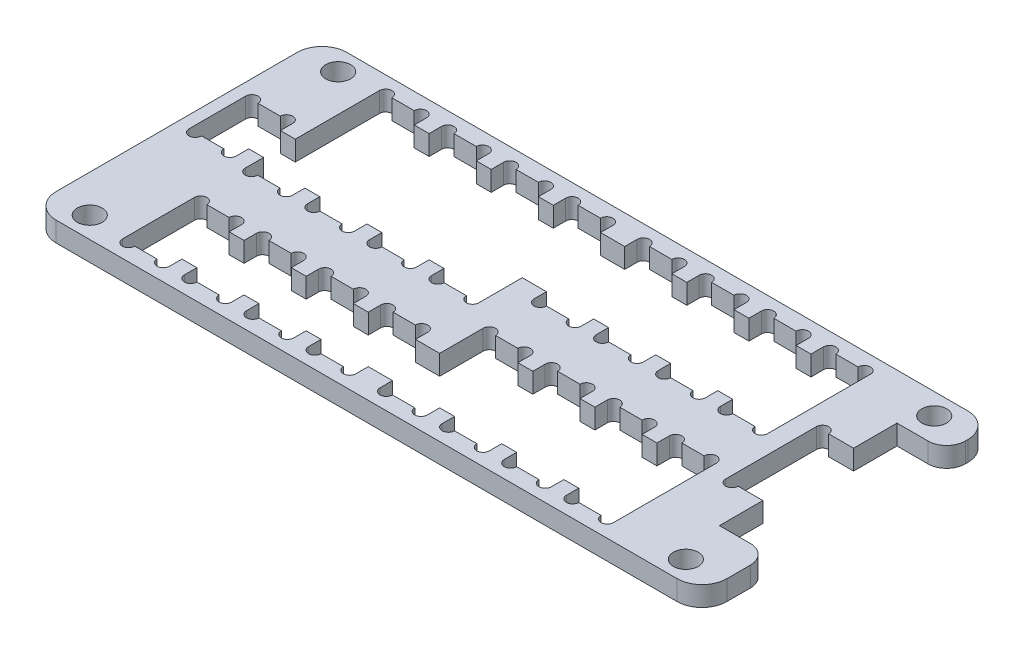
SolidWorks part; units mm, degrees
ref_plane "Plan de face" through (0, 0, 0) normal (0, 0, 1) x (1, 0, 0)
ref_plane "Plan de dessus" through (0, 0, 0) normal (0, 1, 0) x (1, 0, 0)
ref_plane "Plan de droite" through (0, 0, 0) normal (1, 0, 0) x (0, 0, -1)
sketch "Esquisse1" plane through (0, 0, 0) normal (0, 1, 0) x (1, 0, 0)
  line L0 (-151, -90) -> (-97, -90) construction
  line L1 (-124, -78.3) -> (-124, -101.7) construction
  line L3 (-149, -101.7) -> (-99, -101.7)
  line L4 (-151, -99.7) -> (-151, -80.3)
  line L5 (-149, -78.3) -> (-99, -78.3)
  line L6 (-97, -99.7) -> (-97, -80.3)
  line L7 (-151, -101.7) -> (-97, -78.3) construction
  line L8 (-151, -78.3) -> (-97, -101.7) construction
  circle A0 centre (-100, -80) radius 1
  circle A1 centre (-100, -100) radius 1
  circle A2 centre (-148, -100) radius 1
  circle A3 centre (-148, -80) radius 1
  arc A4 (-151, -99.7) -> (-149, -101.7) centre (-149, -99.7) ccw
  arc A5 (-99, -101.7) -> (-97, -99.7) centre (-99, -99.7) ccw
  arc A6 (-97, -80.3) -> (-99, -78.3) centre (-99, -80.3) ccw
  arc A7 (-149, -78.3) -> (-151, -80.3) centre (-149, -80.3) ccw
  point P14 (-124, -90)
  dimension "D5" = 2
  dimension "D8" = 2
  dimension "D1" = 48
  dimension "D2" = 20
  dimension "D3" = 23.4
  dimension "D4" = 54
  dimension "D6" = 80
  dimension "D7" = 148
extrude "base" add sketch "Esquisse1" along normal blind 1.6
sketch "Esquisse2" plane through (0, 0, 0) normal (0, 1, 0) x (1, 0, 0)
  line L0 (-147.35, -85.625) -> (-147.35, -89.875) construction
  line L1 (-147.227, -89.975) -> (-149.023, -89.975)
  line L2 (-146.225, -89.975) -> (-146.225, -85.425)
  line L3 (-147.227, -85.425) -> (-149.023, -85.425)
  line L4 (-150.025, -89.975) -> (-150.025, -85.425)
  line L5 (-146.225, -87.7) -> (-150.025, -87.7) construction
  line L6 (-142.35, -68.9568) -> (-142.35, -111.0917) construction
  line L7 (-141.225, -97.45) -> (-145.025, -97.45) construction
  line L8 (-144.023, -79.65) -> (-142.227, -79.65)
  line L9 (-145.025, -79.65) -> (-145.025, -90.45)
  line L10 (-144.023, -90.45) -> (-142.227, -90.45)
  line L11 (-141.225, -79.65) -> (-141.225, -90.45)
  line L12 (-144.023, -94.55) -> (-142.227, -94.55)
  line L13 (-145.025, -94.55) -> (-145.025, -100.35)
  line L14 (-144.023, -100.35) -> (-142.227, -100.35)
  line L15 (-141.225, -94.55) -> (-141.225, -100.35)
  line L16 (-141.225, -85.05) -> (-145.025, -85.05) construction
  line L17 (-143.125, -90.3) -> (-143.125, -88.6205) construction
  line L18 (-143.125, -100.2) -> (-143.125, -98.5773) construction
  line L19 (-136.225, -79.65) -> (-136.225, -90.45)
  line L20 (-139.023, -90.45) -> (-137.227, -90.45)
  line L21 (-140.025, -79.65) -> (-140.025, -90.45)
  line L22 (-139.023, -79.65) -> (-137.227, -79.65)
  line L23 (-136.225, -94.55) -> (-136.225, -100.35)
  line L24 (-139.023, -100.35) -> (-137.227, -100.35)
  line L25 (-140.025, -94.55) -> (-140.025, -100.35)
  line L26 (-139.023, -94.55) -> (-137.227, -94.55)
  line L27 (-131.225, -79.65) -> (-131.225, -90.45)
  line L28 (-134.023, -90.45) -> (-132.227, -90.45)
  line L29 (-135.025, -79.65) -> (-135.025, -90.45)
  line L30 (-134.023, -79.65) -> (-132.227, -79.65)
  line L31 (-131.225, -94.55) -> (-131.225, -100.35)
  line L32 (-134.023, -100.35) -> (-132.227, -100.35)
  line L33 (-135.025, -94.55) -> (-135.025, -100.35)
  line L34 (-134.023, -94.55) -> (-132.227, -94.55)
  line L35 (-126.225, -79.65) -> (-126.225, -90.45)
  line L36 (-129.023, -90.45) -> (-127.227, -90.45)
  line L37 (-130.025, -79.65) -> (-130.025, -90.45)
  line L38 (-129.023, -79.65) -> (-127.227, -79.65)
  line L39 (-126.225, -94.55) -> (-126.225, -100.35)
  line L40 (-129.023, -100.35) -> (-127.227, -100.35)
  line L41 (-130.025, -94.55) -> (-130.025, -100.35)
  line L42 (-129.023, -94.55) -> (-127.227, -94.55)
  line L43 (-141.225, -79.65) -> (-136.225, -79.65) construction
  line L44 (-121.6, -78.3) -> (-121.6, -101.7) construction
  line L45 (-99, -78.3) -> (-149, -78.3) construction
  line L46 (-149, -101.7) -> (-99, -101.7) construction
  line L47 (-121.6, -90) -> (-105.675, -90) construction
  line L48 (-122.375, -79.65) -> (-122.375, -82.0443) construction
  line L49 (-121.477, -79.65) -> (-123.273, -79.65)
  line L50 (-120.475, -79.65) -> (-120.475, -87.95)
  line L51 (-121.477, -87.95) -> (-123.273, -87.95)
  line L52 (-124.275, -79.65) -> (-124.275, -87.95)
  line L53 (-124.275, -83.8) -> (-120.475, -83.8) construction
  line L54 (-121.477, -100.35) -> (-123.273, -100.35)
  line L55 (-124.275, -100.35) -> (-124.275, -92.05)
  line L56 (-121.477, -92.05) -> (-123.273, -92.05)
  line L57 (-120.475, -100.35) -> (-120.475, -92.05)
  line L58 (-119.275, -79.65) -> (-119.275, -87.95)
  line L59 (-116.477, -87.95) -> (-118.273, -87.95)
  line L60 (-115.475, -79.65) -> (-115.475, -87.95)
  line L61 (-116.477, -79.65) -> (-118.273, -79.65)
  line L62 (-119.275, -100.35) -> (-119.275, -92.05)
  line L63 (-116.477, -92.05) -> (-118.273, -92.05)
  line L64 (-115.475, -100.35) -> (-115.475, -92.05)
  line L65 (-116.477, -100.35) -> (-118.273, -100.35)
  line L66 (-114.275, -79.65) -> (-114.275, -87.95)
  line L67 (-111.477, -87.95) -> (-113.273, -87.95)
  line L68 (-110.475, -79.65) -> (-110.475, -87.95)
  line L69 (-111.477, -79.65) -> (-113.273, -79.65)
  line L70 (-114.275, -100.35) -> (-114.275, -92.05)
  line L71 (-111.477, -92.05) -> (-113.273, -92.05)
  line L72 (-110.475, -100.35) -> (-110.475, -92.05)
  line L73 (-111.477, -100.35) -> (-113.273, -100.35)
  line L74 (-109.275, -79.65) -> (-109.275, -87.95)
  line L75 (-106.477, -87.95) -> (-108.273, -87.95)
  line L76 (-105.475, -79.65) -> (-105.475, -87.95)
  line L77 (-106.477, -79.65) -> (-108.273, -79.65)
  line L78 (-109.275, -100.35) -> (-109.275, -92.05)
  line L79 (-106.477, -92.05) -> (-108.273, -92.05)
  line L80 (-105.475, -100.35) -> (-105.475, -92.05)
  line L81 (-106.477, -100.35) -> (-108.273, -100.35)
  line L82 (-124.275, -79.65) -> (-119.275, -79.65) construction
  line L83 (-97, -99.7) -> (-97, -80.3) construction
  line L84 (-100.998, -85.5) -> (-102.998, -85.5)
  line L85 (-97, -80.5) -> (-97, -97.8)
  line L86 (-100.998, -92.8) -> (-102.998, -92.8)
  line L87 (-104, -85.5) -> (-104, -92.8)
  line L88 (-104, -89.15) -> (-97, -89.15) construction
  line L89 (-100.9, -85.5) -> (-100.9, -92.8) construction
  line L90 (-147.35, -86.6711) -> (-150.025, -86.6711) construction
  line L91 (-142.35, -96.0769) -> (-145.025, -96.0769) construction
  line L92 (-121.6, -84.5733) -> (-124.275, -84.5733) construction
  line L93 (-100.998, -85.5) -> (-100.998, -82)
  line L94 (-100.998, -82) -> (-98.5, -82)
  line L95 (-97, -99.7) -> (-97, -80.3) construction
  line L97 (-100.998, -96.3) -> (-98.5, -96.3)
  line L98 (-100.998, -92.8) -> (-100.998, -96.3)
  arc A0 (-150.025, -85.425) -> (-149.023, -85.425) centre (-149.524, -85.425) cw
  arc A1 (-146.225, -85.425) -> (-147.227, -85.425) centre (-146.726, -85.425) ccw
  arc A2 (-146.225, -89.975) -> (-147.227, -89.975) centre (-146.726, -89.975) cw
  arc A3 (-150.025, -89.975) -> (-149.023, -89.975) centre (-149.524, -89.975) ccw
  arc A4 (-145.025, -79.65) -> (-144.023, -79.65) centre (-144.524, -79.65) cw
  arc A5 (-141.225, -79.65) -> (-142.227, -79.65) centre (-141.726, -79.65) ccw
  arc A6 (-145.025, -90.45) -> (-144.023, -90.45) centre (-144.524, -90.45) ccw
  arc A7 (-141.225, -90.45) -> (-142.227, -90.45) centre (-141.726, -90.45) cw
  arc A8 (-145.025, -94.55) -> (-144.023, -94.55) centre (-144.524, -94.55) cw
  arc A9 (-141.225, -94.55) -> (-142.227, -94.55) centre (-141.726, -94.55) ccw
  arc A10 (-145.025, -100.35) -> (-144.023, -100.35) centre (-144.524, -100.35) ccw
  arc A11 (-141.225, -100.35) -> (-142.227, -100.35) centre (-141.726, -100.35) cw
  arc A12 (-136.225, -90.45) -> (-137.227, -90.45) centre (-136.726, -90.45) cw
  arc A13 (-140.025, -90.45) -> (-139.023, -90.45) centre (-139.524, -90.45) ccw
  arc A14 (-140.025, -79.65) -> (-139.023, -79.65) centre (-139.524, -79.65) cw
  arc A15 (-136.225, -79.65) -> (-137.227, -79.65) centre (-136.726, -79.65) ccw
  arc A16 (-136.225, -100.35) -> (-137.227, -100.35) centre (-136.726, -100.35) cw
  arc A17 (-140.025, -100.35) -> (-139.023, -100.35) centre (-139.524, -100.35) ccw
  arc A18 (-140.025, -94.55) -> (-139.023, -94.55) centre (-139.524, -94.55) cw
  arc A19 (-136.225, -94.55) -> (-137.227, -94.55) centre (-136.726, -94.55) ccw
  arc A20 (-131.225, -90.45) -> (-132.227, -90.45) centre (-131.726, -90.45) cw
  arc A21 (-135.025, -90.45) -> (-134.023, -90.45) centre (-134.524, -90.45) ccw
  arc A22 (-135.025, -79.65) -> (-134.023, -79.65) centre (-134.524, -79.65) cw
  arc A23 (-131.225, -79.65) -> (-132.227, -79.65) centre (-131.726, -79.65) ccw
  arc A24 (-131.225, -100.35) -> (-132.227, -100.35) centre (-131.726, -100.35) cw
  arc A25 (-135.025, -100.35) -> (-134.023, -100.35) centre (-134.524, -100.35) ccw
  arc A26 (-135.025, -94.55) -> (-134.023, -94.55) centre (-134.524, -94.55) cw
  arc A27 (-131.225, -94.55) -> (-132.227, -94.55) centre (-131.726, -94.55) ccw
  arc A28 (-126.225, -90.45) -> (-127.227, -90.45) centre (-126.726, -90.45) cw
  arc A29 (-130.025, -90.45) -> (-129.023, -90.45) centre (-129.524, -90.45) ccw
  arc A30 (-130.025, -79.65) -> (-129.023, -79.65) centre (-129.524, -79.65) cw
  arc A31 (-126.225, -79.65) -> (-127.227, -79.65) centre (-126.726, -79.65) ccw
  arc A32 (-126.225, -100.35) -> (-127.227, -100.35) centre (-126.726, -100.35) cw
  arc A33 (-130.025, -100.35) -> (-129.023, -100.35) centre (-129.524, -100.35) ccw
  arc A34 (-130.025, -94.55) -> (-129.023, -94.55) centre (-129.524, -94.55) cw
  arc A35 (-126.225, -94.55) -> (-127.227, -94.55) centre (-126.726, -94.55) ccw
  arc A36 (-124.275, -79.65) -> (-123.273, -79.65) centre (-123.774, -79.65) cw
  arc A37 (-120.475, -79.65) -> (-121.477, -79.65) centre (-120.976, -79.65) ccw
  arc A38 (-120.475, -87.95) -> (-121.477, -87.95) centre (-120.976, -87.95) cw
  arc A39 (-124.275, -87.95) -> (-123.273, -87.95) centre (-123.774, -87.95) ccw
  arc A40 (-120.475, -100.35) -> (-121.477, -100.35) centre (-120.976, -100.35) cw
  arc A41 (-124.275, -100.35) -> (-123.273, -100.35) centre (-123.774, -100.35) ccw
  arc A42 (-124.275, -92.05) -> (-123.273, -92.05) centre (-123.774, -92.05) cw
  arc A43 (-120.475, -92.05) -> (-121.477, -92.05) centre (-120.976, -92.05) ccw
  arc A44 (-119.275, -87.95) -> (-118.273, -87.95) centre (-118.774, -87.95) ccw
  arc A45 (-115.475, -87.95) -> (-116.477, -87.95) centre (-115.976, -87.95) cw
  arc A46 (-115.475, -79.65) -> (-116.477, -79.65) centre (-115.976, -79.65) ccw
  arc A47 (-119.275, -79.65) -> (-118.273, -79.65) centre (-118.774, -79.65) cw
  arc A48 (-119.275, -92.05) -> (-118.273, -92.05) centre (-118.774, -92.05) cw
  arc A49 (-115.475, -92.05) -> (-116.477, -92.05) centre (-115.976, -92.05) ccw
  arc A50 (-115.475, -100.35) -> (-116.477, -100.35) centre (-115.976, -100.35) cw
  arc A51 (-119.275, -100.35) -> (-118.273, -100.35) centre (-118.774, -100.35) ccw
  arc A52 (-114.275, -87.95) -> (-113.273, -87.95) centre (-113.774, -87.95) ccw
  arc A53 (-110.475, -87.95) -> (-111.477, -87.95) centre (-110.976, -87.95) cw
  arc A54 (-110.475, -79.65) -> (-111.477, -79.65) centre (-110.976, -79.65) ccw
  arc A55 (-114.275, -79.65) -> (-113.273, -79.65) centre (-113.774, -79.65) cw
  arc A56 (-114.275, -92.05) -> (-113.273, -92.05) centre (-113.774, -92.05) cw
  arc A57 (-110.475, -92.05) -> (-111.477, -92.05) centre (-110.976, -92.05) ccw
  arc A58 (-110.475, -100.35) -> (-111.477, -100.35) centre (-110.976, -100.35) cw
  arc A59 (-114.275, -100.35) -> (-113.273, -100.35) centre (-113.774, -100.35) ccw
  arc A60 (-109.275, -87.95) -> (-108.273, -87.95) centre (-108.774, -87.95) ccw
  arc A61 (-105.475, -87.95) -> (-106.477, -87.95) centre (-105.976, -87.95) cw
  arc A62 (-105.475, -79.65) -> (-106.477, -79.65) centre (-105.976, -79.65) ccw
  arc A63 (-109.275, -79.65) -> (-108.273, -79.65) centre (-108.774, -79.65) cw
  arc A64 (-109.275, -92.05) -> (-108.273, -92.05) centre (-108.774, -92.05) cw
  arc A65 (-105.475, -92.05) -> (-106.477, -92.05) centre (-105.976, -92.05) ccw
  arc A66 (-105.475, -100.35) -> (-106.477, -100.35) centre (-105.976, -100.35) cw
  arc A67 (-109.275, -100.35) -> (-108.273, -100.35) centre (-108.774, -100.35) ccw
  arc A68 (-104, -85.5) -> (-102.998, -85.5) centre (-103.499, -85.5) cw
  arc A69 (-104, -92.8) -> (-102.998, -92.8) centre (-103.499, -92.8) ccw
  arc A70 (-98.5, -82) -> (-97, -80.5) centre (-98.5, -80.5) ccw
  arc A71 (-98.5, -96.3) -> (-97, -97.8) centre (-98.5, -97.8) cw
  point P152 (-122.375, -87.95)
  point P264 (-97, -81.1652)
  point P266 (-97, -81.3019)
  point P267 (0, 0)
  point P271 (0, 0)
  dimension "D13" = 0.501
  dimension "D26" = 1.5
  dimension "D1" = 4.55
  dimension "D2" = 2.675
  dimension "D3" = 3.8
  dimension "D4" = 147.35
  dimension "D5" = 87.7
  dimension "D6" = 142.35
  dimension "D7" = 4
  dimension "D8" = 1.125
  dimension "D9" = 5.8
  dimension "D10" = 10.8
  dimension "D11" = 85.05
  dimension "D12" = 97.45
  dimension "D14" = 5
  dimension "D15" = 121.6
  dimension "D16" = 8.3
  dimension "D17" = 4
  dimension "D18" = 83.8
  dimension "D19" = 2
  dimension "D20" = 5
  dimension "D21" = 89.15
  dimension "D22" = 100.9
  dimension "D23" = 3.1
  dimension "D24" = 7.3
  dimension "D25" = 3.5
extrude "trous molex" cut sketch "Esquisse2" along normal through all
sketch "Esquisse3" plane through (0, 0, 0) normal (0, 1, 0) x (1, 0, 0)
  line L0 (-146.225, -87.7) -> (-145.025, -87.7) construction
  line L1 (-146.225, -89.975) -> (-146.225, -85.425) construction
  line L2 (-145.025, -79.65) -> (-145.025, -90.45) construction
  line L3 (-141.225, -97.45) -> (-140.025, -97.45) construction
  line L4 (-146.225, -86.425) -> (-145.025, -86.425)
  line L5 (-146.225, -86.425) -> (-146.225, -88.975)
  line L6 (-146.225, -88.975) -> (-145.025, -88.975)
  line L7 (-145.025, -86.425) -> (-145.025, -88.975)
  line L8 (-146.225, -86.425) -> (-145.025, -88.975) construction
  line L9 (-146.225, -88.975) -> (-145.025, -86.425) construction
  line L10 (-141.225, -100.35) -> (-141.225, -94.55) construction
  line L11 (-140.025, -94.55) -> (-140.025, -100.35) construction
  line L12 (-136.225, -99.35) -> (-135.025, -99.35)
  line L13 (-141.225, -95.55) -> (-140.025, -95.55)
  line L14 (-141.225, -95.55) -> (-141.225, -99.35)
  line L15 (-141.225, -99.35) -> (-140.025, -99.35)
  line L16 (-140.025, -95.55) -> (-140.025, -99.35)
  line L17 (-141.225, -95.55) -> (-140.025, -99.35) construction
  line L18 (-141.225, -99.35) -> (-140.025, -95.55) construction
  line L19 (-135.025, -95.55) -> (-135.025, -99.35)
  line L20 (-136.225, -95.55) -> (-135.025, -95.55)
  line L21 (-136.225, -95.55) -> (-136.225, -99.35)
  line L22 (-131.225, -99.35) -> (-130.025, -99.35)
  line L23 (-130.025, -95.55) -> (-130.025, -99.35)
  line L24 (-131.225, -95.55) -> (-130.025, -95.55)
  line L25 (-131.225, -95.55) -> (-131.225, -99.35)
  line L26 (-141.225, -99.35) -> (-136.225, -99.35) construction
  line L27 (-141.225, -85.05) -> (-140.025, -85.05) construction
  line L28 (-141.225, -90.45) -> (-141.225, -79.65) construction
  line L29 (-140.025, -79.65) -> (-140.025, -90.45) construction
  line L30 (-135.025, -80.65) -> (-135.025, -89.45)
  line L31 (-141.225, -80.65) -> (-140.025, -80.65)
  line L32 (-141.225, -80.65) -> (-141.225, -89.45)
  line L33 (-141.225, -89.45) -> (-140.025, -89.45)
  line L34 (-140.025, -80.65) -> (-140.025, -89.45)
  line L35 (-141.225, -80.65) -> (-140.025, -89.45) construction
  line L36 (-141.225, -89.45) -> (-140.025, -80.65) construction
  line L37 (-136.225, -89.45) -> (-135.025, -89.45)
  line L38 (-136.225, -80.65) -> (-136.225, -89.45)
  line L39 (-136.225, -80.65) -> (-135.025, -80.65)
  line L40 (-130.025, -80.65) -> (-130.025, -89.45)
  line L41 (-131.225, -89.45) -> (-130.025, -89.45)
  line L42 (-131.225, -80.65) -> (-131.225, -89.45)
  line L43 (-131.225, -80.65) -> (-130.025, -80.65)
  line L44 (-140.025, -80.65) -> (-135.025, -80.65) construction
  line L45 (-120.475, -83.8) -> (-119.275, -83.8) construction
  line L46 (-120.475, -87.95) -> (-120.475, -79.65) construction
  line L47 (-119.275, -79.65) -> (-119.275, -87.95) construction
  line L48 (-151, -90) -> (-98.1538, -90) construction
  line L49 (-120.475, -80.65) -> (-119.275, -80.65)
  line L50 (-120.475, -80.65) -> (-120.475, -86.95)
  line L51 (-120.475, -86.95) -> (-119.275, -86.95)
  line L52 (-119.275, -80.65) -> (-119.275, -86.95)
  line L53 (-120.475, -80.65) -> (-119.275, -86.95) construction
  line L54 (-120.475, -86.95) -> (-119.275, -80.65) construction
  line L55 (-151, -80.3) -> (-151, -99.7) construction
  line L56 (-120.475, -99.35) -> (-120.475, -93.05)
  line L57 (-120.475, -99.35) -> (-119.275, -99.35)
  line L58 (-119.275, -99.35) -> (-119.275, -93.05)
  line L59 (-120.475, -93.05) -> (-119.275, -93.05)
  line L60 (-115.475, -86.95) -> (-114.275, -86.95)
  line L61 (-114.275, -80.65) -> (-114.275, -86.95)
  line L62 (-115.475, -80.65) -> (-114.275, -80.65)
  line L63 (-115.475, -80.65) -> (-115.475, -86.95)
  line L64 (-115.475, -93.05) -> (-114.275, -93.05)
  line L65 (-114.275, -99.35) -> (-114.275, -93.05)
  line L66 (-115.475, -99.35) -> (-114.275, -99.35)
  line L67 (-115.475, -99.35) -> (-115.475, -93.05)
  line L68 (-110.475, -86.95) -> (-109.275, -86.95)
  line L69 (-109.275, -80.65) -> (-109.275, -86.95)
  line L70 (-110.475, -80.65) -> (-109.275, -80.65)
  line L71 (-110.475, -80.65) -> (-110.475, -86.95)
  line L72 (-110.475, -93.05) -> (-109.275, -93.05)
  line L73 (-109.275, -99.35) -> (-109.275, -93.05)
  line L74 (-110.475, -99.35) -> (-109.275, -99.35)
  line L75 (-110.475, -99.35) -> (-110.475, -93.05)
  line L76 (-120.475, -86.95) -> (-115.475, -86.95) construction
  line L77 (-126.225, -97.45) -> (-124.275, -97.45) construction
  line L78 (-126.225, -100.35) -> (-126.225, -94.55) construction
  line L79 (-124.275, -92.05) -> (-124.275, -100.35) construction
  line L80 (-124.275, -83.8) -> (-126.225, -83.8) construction
  line L81 (-126.225, -95.55) -> (-124.275, -95.55)
  line L82 (-126.225, -95.55) -> (-126.225, -99.35)
  line L83 (-126.225, -99.35) -> (-124.275, -99.35)
  line L84 (-124.275, -95.55) -> (-124.275, -99.35)
  line L85 (-126.225, -95.55) -> (-124.275, -99.35) construction
  line L86 (-126.225, -99.35) -> (-124.275, -95.55) construction
  line L87 (-124.275, -79.65) -> (-124.275, -87.95) construction
  line L88 (-126.225, -90.45) -> (-126.225, -79.65) construction
  line L90 (-126.225, -80.65) -> (-124.275, -80.65)
  line L91 (-126.225, -80.65) -> (-126.225, -86.95)
  line L92 (-126.225, -86.95) -> (-124.275, -86.95)
  line L93 (-124.275, -80.65) -> (-124.275, -86.95)
  line L94 (-126.225, -80.65) -> (-124.275, -86.95) construction
  line L95 (-126.225, -86.95) -> (-124.275, -80.65) construction
  point P6 (-145.625, -87.7)
  point P18 (-140.625, -97.45)
  point P40 (-140.625, -85.05)
  point P62 (-119.875, -83.8)
  point P100 (-125.25, -97.45)
  point P111 (-125.25, -83.8)
  dimension "D1" = 1
  dimension "D2" = 1
  dimension "D3" = 5
  dimension "D4" = 1
  dimension "D5" = 5
  dimension "D6" = 1
  dimension "D7" = 5
  dimension "D9" = 3
  dimension "D8" = 3
extrude "Enlèv. mat.-Extru.4" cut sketch "Esquisse3" along normal through all
